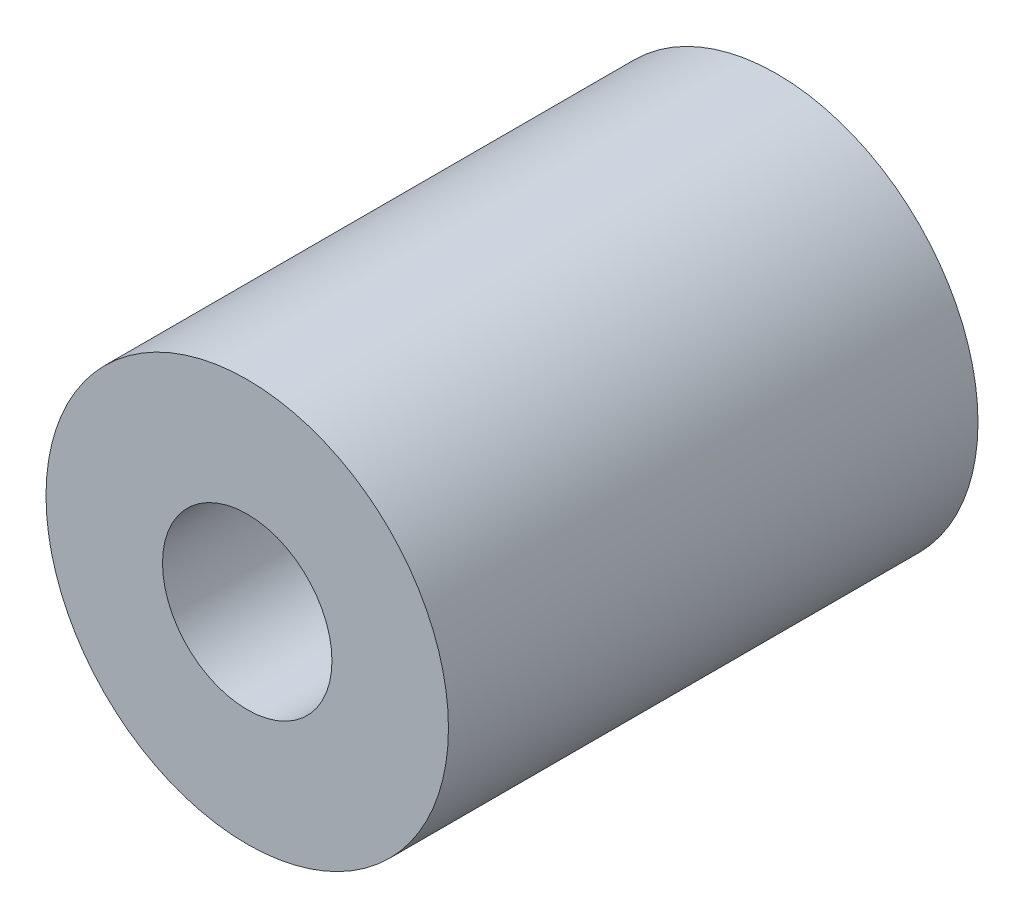
SolidWorks part; units mm, degrees
ref_plane "Front Plane" through (0, 0, 0) normal (0, 0, 1) x (1, 0, 0)
ref_plane "Top Plane" through (0, 0, 0) normal (0, 1, 0) x (1, 0, 0)
ref_plane "Right Plane" through (0, 0, 0) normal (1, 0, 0) x (0, 0, -1)
sketch "Sketch1" plane through (0, 0, 0) normal (0, 0, 1) x (1, 0, 0)
  circle A0 centre (0, 0) radius 9.5
extrude "Boss-Extrude1" add sketch "Sketch1" along normal blind 25
sketch "Sketch2" plane through (0, 0, 25) normal (0, 0, 1) x (1, 0, 0)
  circle A0 centre (0, 0) radius 4
extrude "Cut-Extrude1" cut sketch "Sketch2" against normal blind 10
sketch "Sketch3" plane through (0, 0, 0) normal (0, 0, -1) x (-1, 0, 0)
  circle A0 centre (0, 0) radius 2.5
extrude "Cut-Extrude2" cut sketch "Sketch3" against normal blind 10
